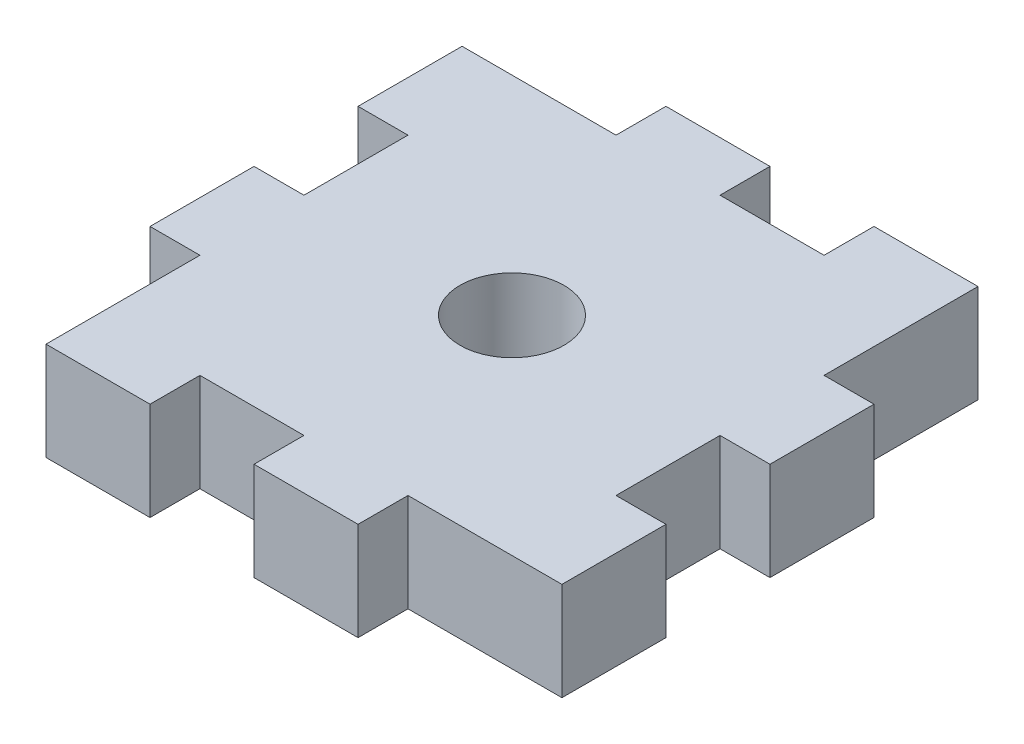
SolidWorks part; units mm, degrees
material "Acrylic (Medium-high impact)"
ref_plane "Front Plane" through (0, 0, 0) normal (0, 0, 1) x (1, 0, 0)
ref_plane "Top Plane" through (0, 0, 0) normal (0, 1, 0) x (1, 0, 0)
ref_plane "Right Plane" through (0, 0, 0) normal (1, 0, 0) x (0, 0, -1)
sketch "Sketch1" plane through (0, 0, 0) normal (0, 1, 0) x (1, 0, 0)
  line L0 (28.448, 3.048) -> (19.05, 3.048)
  line L1 (19.05, 3.048) -> (19.05, 0)
  line L2 (19.05, 0) -> (12.7, 0)
  line L3 (12.7, 0) -> (12.7, 3.048)
  line L4 (12.7, 3.048) -> (6.35, 3.048)
  line L5 (6.35, 3.048) -> (6.35, 0)
  line L6 (6.35, 0) -> (0, 0)
  line L7 (0, 0) -> (0, 9.398)
  line L8 (0, 9.398) -> (-3.048, 9.398)
  line L9 (-3.048, 9.398) -> (-3.048, 15.748)
  line L10 (-3.048, 15.748) -> (0, 15.748)
  line L11 (0, 15.748) -> (0, 22.098)
  line L12 (0, 22.098) -> (-3.048, 22.098)
  line L13 (-3.048, 22.098) -> (-3.048, 28.448)
  line L14 (-3.048, 28.448) -> (6.35, 28.448)
  line L15 (6.35, 28.448) -> (6.35, 31.496)
  line L16 (6.35, 31.496) -> (12.7, 31.496)
  line L17 (12.7, 31.496) -> (12.7, 28.448)
  line L18 (12.7, 28.448) -> (19.05, 28.448)
  line L19 (19.05, 28.448) -> (19.05, 31.496)
  line L20 (19.05, 31.496) -> (25.4, 31.496)
  line L21 (25.4, 31.496) -> (25.4, 22.098)
  line L22 (25.4, 22.098) -> (28.448, 22.098)
  line L23 (28.448, 22.098) -> (28.448, 15.748)
  line L24 (28.448, 15.748) -> (25.4, 15.748)
  line L25 (25.4, 15.748) -> (25.4, 9.398)
  line L26 (25.4, 9.398) -> (28.448, 9.398)
  line L27 (28.448, 9.398) -> (28.448, 3.048)
  circle A0 centre (12.7, 15.748) radius 3.175
  dimension "D1" = 6.35
  dimension "D8" = 6.35
  dimension "D2" = 9.398
  dimension "D3" = 6.35
  dimension "D4" = 6.35
  dimension "D5" = 6.35
  dimension "D6" = 3.048
  dimension "D7" = 9.398
extrude "Boss-Extrude1" add sketch "Sketch1" along normal blind 5.9944
